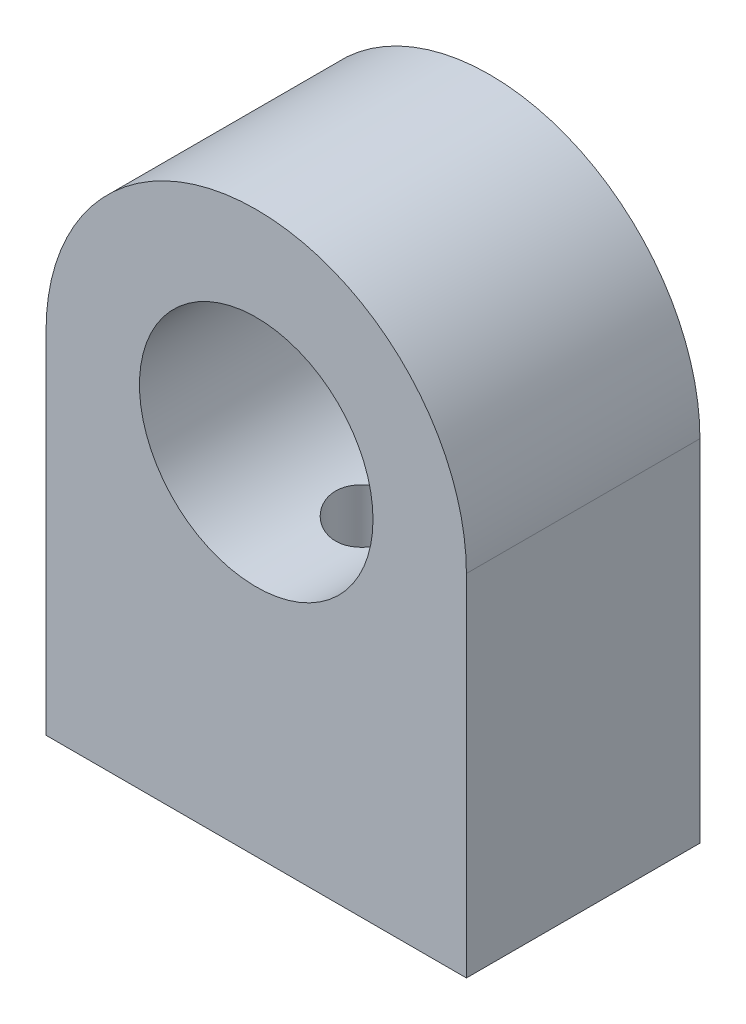
SolidWorks part; units mm, degrees
ref_plane "Front Plane" through (0, 0, 0) normal (0, 0, 1) x (1, 0, 0)
ref_plane "Top Plane" through (0, 0, 0) normal (0, 1, 0) x (1, 0, 0)
ref_plane "Right Plane" through (0, 0, 0) normal (1, 0, 0) x (0, 0, -1)
sketch "Sketch1" plane through (0, 0, 0) normal (0, 0, 1) x (1, 0, 0)
  line L1 (-5.715, -9.525) -> (5.715, -9.525)
  line L2 (-5.715, -9.525) -> (-5.715, 0)
  line L4 (5.715, -9.525) -> (5.715, 0)
  circle A0 centre (0, 0) radius 3.175
  arc A3 (5.715, 0) -> (-5.715, 0) centre (0, 0) ccw
  point P5 (0, -4.7625)
  point P11 (0, 0)
  dimension "D1" = 6.35
  dimension "D2" = 9.525
extrude "Boss-Extrude1" add sketch "Sketch1" along normal blind 6.35
sketch "Sketch2" plane through (0, -9.525, 0) normal (0, -1, 0) x (1, 0, 0)
  line L1 (0, 3.175) -> (5.715, 3.175)
  line L2 (5.715, 6.35) -> (5.715, 0) construction
  circle A0 centre (0, 3.175) radius 1.016
  point P2 (0, 0)
  dimension "D1" = 2.032
extrude "Cut-Extrude1" cut sketch "Sketch2" against normal blind 9.144 contours A0
